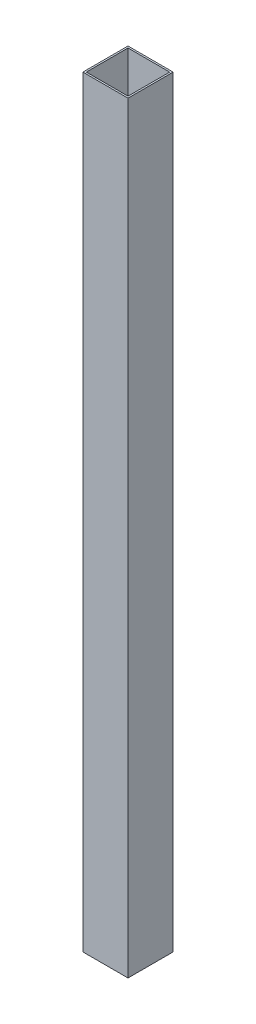
SolidWorks part; units mm, degrees
material "6061-T6 (SS)"
ref_plane "Front Plane" through (0, 0, 0) normal (0, 0, 1) x (1, 0, 0)
ref_plane "Top Plane" through (0, 0, 0) normal (0, 1, 0) x (1, 0, 0)
ref_plane "Right Plane" through (0, 0, 0) normal (1, 0, 0) x (0, 0, -1)
sketch "Sketch1" plane through (0, 0, 0) normal (0, 1, 0) x (1, 0, 0)
  line L0 (-11.7348, -11.7348) -> (11.7348, -11.7348)
  line L1 (-12.7, 12.7) -> (12.7, 12.7)
  line L2 (-12.7, 12.7) -> (-12.7, -12.7)
  line L3 (-12.7, -12.7) -> (12.7, -12.7)
  line L4 (12.7, 12.7) -> (12.7, -12.7)
  line L5 (-12.7, 12.7) -> (12.7, -12.7) construction
  line L6 (-12.7, -12.7) -> (12.7, 12.7) construction
  line L7 (11.7348, 11.7348) -> (11.7348, -11.7348)
  line L8 (-11.7348, 11.7348) -> (11.7348, 11.7348)
  line L9 (-11.7348, 11.7348) -> (-11.7348, -11.7348)
  point P0 (0, 0)
  dimension "D1" = 25.4
  dimension "D2" = 25.4
  dimension "D3" = 0.9652
extrude "Boss-Extrude1" add sketch "Sketch1" along normal blind 428.625
